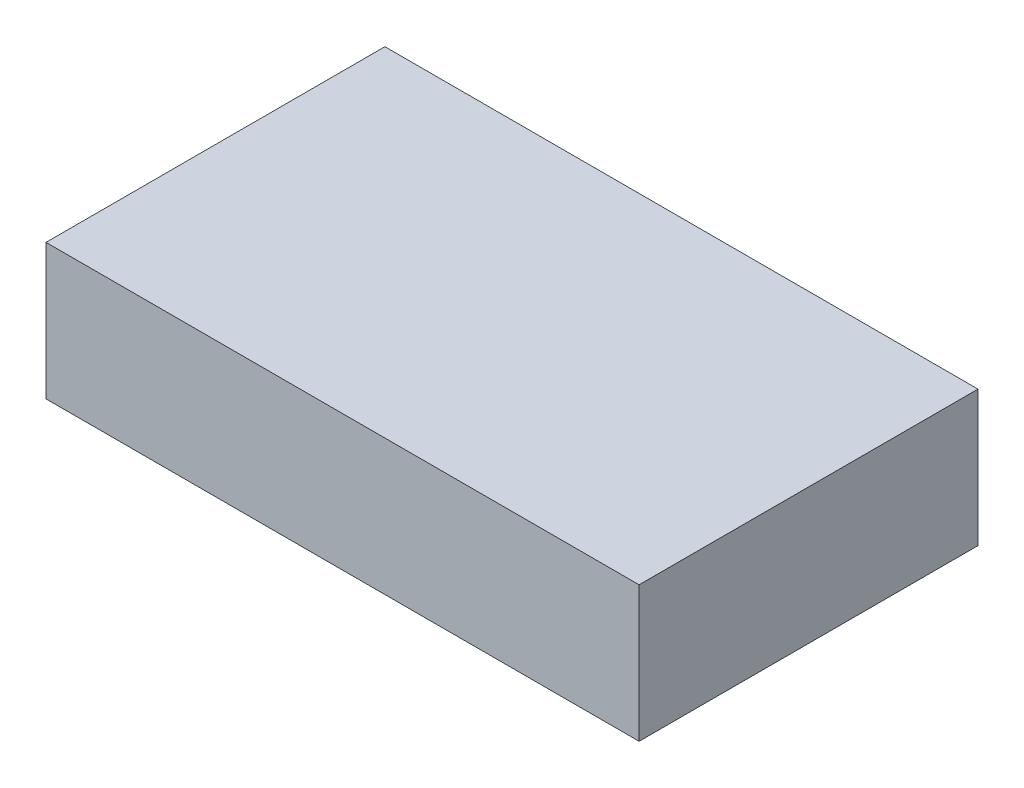
SolidWorks part; units mm, degrees
ref_plane "Front Plane" through (0, 0, 0) normal (0, 0, 1) x (1, 0, 0)
ref_plane "Top Plane" through (0, 0, 0) normal (0, 1, 0) x (1, 0, 0)
ref_plane "Right Plane" through (0, 0, 0) normal (1, 0, 0) x (0, 0, -1)
sketch "Sketch1" plane through (0, 0, 0) normal (0, 1, 0) x (1, 0, 0)
  line L1 (-17.5, -10) -> (17.5, -10)
  line L2 (-17.5, -10) -> (-17.5, 10)
  line L3 (-17.5, 10) -> (17.5, 10)
  line L4 (17.5, -10) -> (17.5, 10)
  line L5 (-17.5, -10) -> (17.5, 10) construction
  line L6 (-17.5, 10) -> (17.5, -10) construction
  point P0 (0, 0)
  dimension "D1" = 35
  dimension "D2" = 20
extrude "Boss-Extrude1" add sketch "Sketch1" along normal mid plane 8
